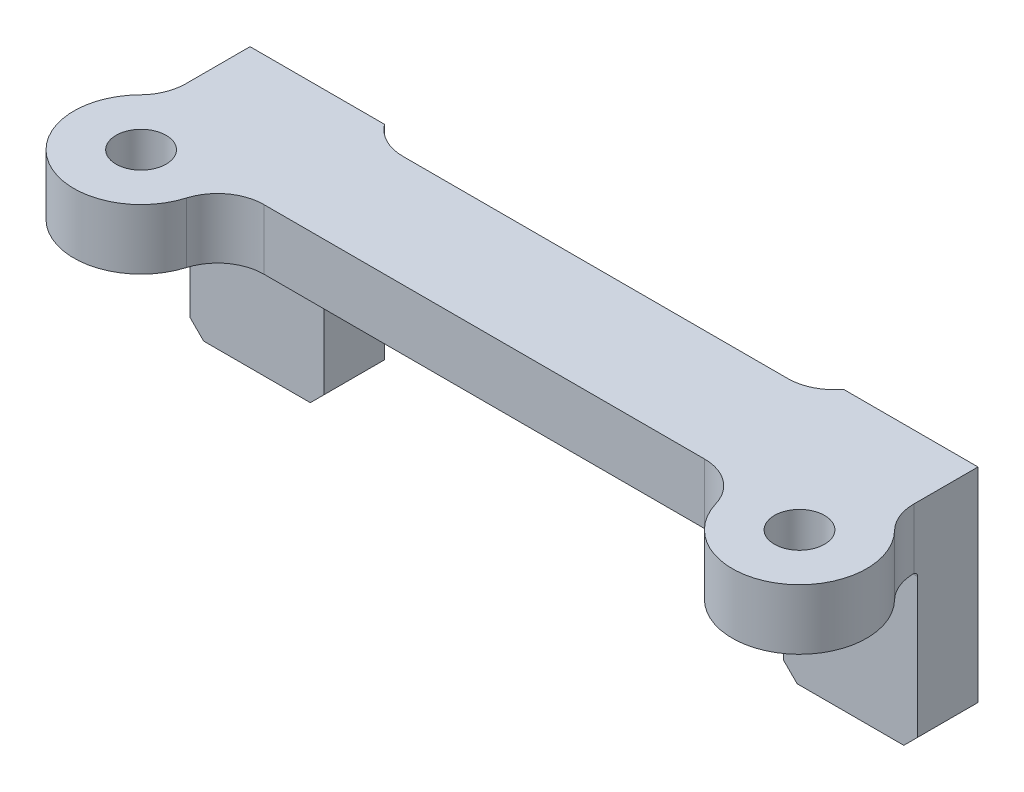
SolidWorks part; units mm, degrees
material "34CrMo4(ISO 683-1)-[T3]"
ref_plane "Front" through (0, 0, 0) normal (0, 0, 1) x (1, 0, 0)
ref_plane "Top" through (0, 0, 0) normal (0, 1, 0) x (1, 0, 0)
ref_plane "Right" through (0, 0, 0) normal (1, 0, 0) x (0, 0, -1)
sketch "Esquisse1" plane through (0, 0, 0) normal (0, 1, 0) x (1, 0, 0)
  line L0 (0, 0) -> (142, 0) construction
  line L1 (71, 0) -> (71, 54.678) construction
  line L2 (-7.5, 31) -> (149.5, 31)
  line L3 (23.4787, 3) -> (118.5213, 3)
  line L6 (-7.5, 31) -> (-7.5, 17.1464)
  line L7 (149.5, 31) -> (149.5, 17.1464)
  arc A2 (-10.3571, 10.1479) -> (13.8956, -4.1429) centre (0, 0) ccw
  arc A3 (128.1044, -4.1429) -> (152.3571, 10.1479) centre (142, 0) ccw
  arc A4 (23.4787, 3) -> (13.8956, -4.1429) centre (23.4787, -7) ccw
  arc A5 (128.1044, -4.1429) -> (118.5213, 3) centre (118.5213, -7) ccw
  arc A6 (152.3571, 10.1479) -> (149.5, 17.1464) centre (159.5, 17.1464) cw
  arc A7 (-7.5, 17.1464) -> (-10.3571, 10.1479) centre (-17.5, 17.1464) cw
  dimension "D1" = 142
  dimension "D2" = 10
  dimension "D3" = 29
  dimension "D6" = 78.5
  dimension "D8" = 10
  dimension "D4" = 28
  dimension "D5" = 31
  dimension "D7" = 157
extrude "Boss.-Extru.1" add sketch "Esquisse1" along normal blind 38 and the other way blind 10
sketch "Esquisse8" plane through (0, -10, 0) normal (0, -1, 0) x (1, 0, 0)
  line L0 (149.5, -31) -> (-7.5, -31) construction
  line L1 (-25, 27) -> (175, 27)
  line L2 (-25, 27) -> (-25, -18)
  line L3 (-25, -18) -> (175, -18)
  line L4 (175, 27) -> (175, -18)
  dimension "D1" = 13
  dimension "D2" = 25
  dimension "D3" = 200
  dimension "D4" = 45
extrude "Enlèv. mat.-Extru.4" cut sketch "Esquisse8" against normal offset from surface (34 mm away) 14 up to face at (71, 38, -8.5931)
hole_wizard "Trou taraudé M14x1.51" positions "Esquisse3" profile "Esquisse4" tap size "M14x1.5" standard "ISO"
sketch "Esquisse3" plane through (0, 0, -31) normal (0, 0, -1) x (-1, 0, 0)
  line L0 (-136, 19.5) -> (-6, 19.5) construction
  line L1 (-71, 19.5) -> (-71, 34.5503) construction
  line L4 (0, 38) -> (0, 24) construction
  line L6 (7.5, 24) -> (-149.5, 24) construction
  point P0 (-136, 19.5)
  point P2 (-6, 19.5)
  dimension "D1" = 130
  dimension "D2" = 4.5
  dimension "D3" = 71
sketch "Esquisse4" plane through (136, 19.5, -31) normal (1, 0, 0) x (0, 1, 0)
  line L0 (0, 0) -> (0, 21.2554)
  line L1 (0, 21.2554) -> (6.25, 17.5)
  line L2 (6.25, 17.5) -> (6.25, 0)
  line L5 (6.25, 0) -> (0, 0)
  line L10 (0, 21.2554) -> (-6.25, 17.5) construction
  line L11 (0, -6.35) -> (0, 107.95) construction
  dimension "Diamètre du trou pour taraudage" = 12.5
  dimension "Profondeur du trou pour taraudage" = 17.5
  dimension "Angle de pointe" = 118
cosmetic thread "Filetage de perçage1" parameters "D1"=15, "D2"=14
cosmetic thread "Filetage de perçage2" parameters "D1"=15, "D2"=14
sketch "Esquisse10" plane through (0, 0, -18) normal (0, 0, 1) x (1, 0, 0)
  line L0 (-7.5, -10) -> (149.5, -10) construction
  line L1 (21.5, -10) -> (120.5, -10)
  line L2 (21.5, -10) -> (21.5, 24)
  line L3 (21.5, 24) -> (120.5, 24)
  line L4 (120.5, -10) -> (120.5, 24)
  line L5 (149.5, 38) -> (149.5, -10) construction
  line L6 (-7.5, 38) -> (-7.5, -10) construction
  line L8 (10.3373, 24) -> (131.6627, 24) construction
  dimension "D1" = 29
  dimension "D2" = 29
  dimension "D3" = 0
extrude "Enlèv. mat.-Extru.6" cut sketch "Esquisse10" against normal through all
fillet "Congé2" radius 10 2 edges at (21.5, 24, -24.5) (120.5, 24, -24.5)
sketch "Esquisse11" plane through (0, 38, 0) normal (0, 1, 0) x (1, 0, 0)
  line L0 (29.5, 27) -> (112.5, 27)
  line L1 (122.5, 37) -> (122.5, 47)
  line L2 (19.5, 37) -> (19.5, 47)
  line L3 (19.5, 47) -> (122.5, 47)
  line L4 (149.5, 31) -> (-7.5, 31) construction
  arc A0 (122.5, 37) -> (112.5, 27) centre (112.5, 37) cw
  arc A1 (19.5, 37) -> (29.5, 27) centre (29.5, 37) ccw
  point P10 (21.5, 31)
  point P12 (120.5, 31)
  dimension "D1" = 10
  dimension "D2" = 4
  dimension "D3" = 29.5
  dimension "D4" = 83
  dimension "D5" = 20
extrude "Enlèv. mat.-Extru.7" cut sketch "Esquisse11" against normal through all both and the other way through all
hole_wizard "Trou taraudé M12x1.251" positions "Esquisse12" profile "Esquisse13" tap size "M12x1.25" standard "ISO" end condition through all
sketch "Esquisse12" plane through (0, 24, 0) normal (0, -1, 0) x (-1, 0, 0)
  point P0 (0, 0)
  point P3 (-142, 0)
sketch "Esquisse13" plane through (0, 24, 0) normal (1, 0, 0) x (0, 0, -1)
  line L0 (0, 0) -> (0, 14.0001)
  line L1 (0, 14.0001) -> (5.4, 14.0001)
  line L2 (5.4, 14.0001) -> (5.4, 0)
  line L5 (5.4, 0) -> (0, 0)
  line L11 (0, -6.35) -> (0, 107.95) construction
  dimension "Diamètre du trou pour taraudage jusqu'au prochain" = 10.8
  dimension "Profondeur du trou pour taraudage jusqu'au prochain" = 14.0001
cosmetic thread "Filetage de perçage3" parameters "D2"=12
cosmetic thread "Filetage de perçage4" parameters "D2"=12
chamfer "Chanfrein1" distance 3 angle 45 4 edges at (21.5, -10, -24.5) (120.5, -10, -24.5) (-7.5, -10, -24.5) (149.5, -10, -24.5)
fillet "Congé3" radius 1 4 edges at (144.9187, 24, -18) (121.0813, 24, -18) (20.9187, 24, -18) (-2.9187, 24, -18)
sketch "Esquisse14" plane through (0, 38, 0) normal (0, 1, 0) x (1, 0, 0)
  line L1 (-34.6405, 45.8659) -> (183.4876, 45.8659)
  line L2 (-34.6405, 45.8659) -> (-34.6405, -32.582)
  line L3 (-34.6405, -32.582) -> (183.4876, -32.582)
  line L4 (183.4876, 45.8659) -> (183.4876, -32.582)
extrude "Enlèv. mat.-Extru.8" cut sketch "Esquisse14" against normal blind 1
